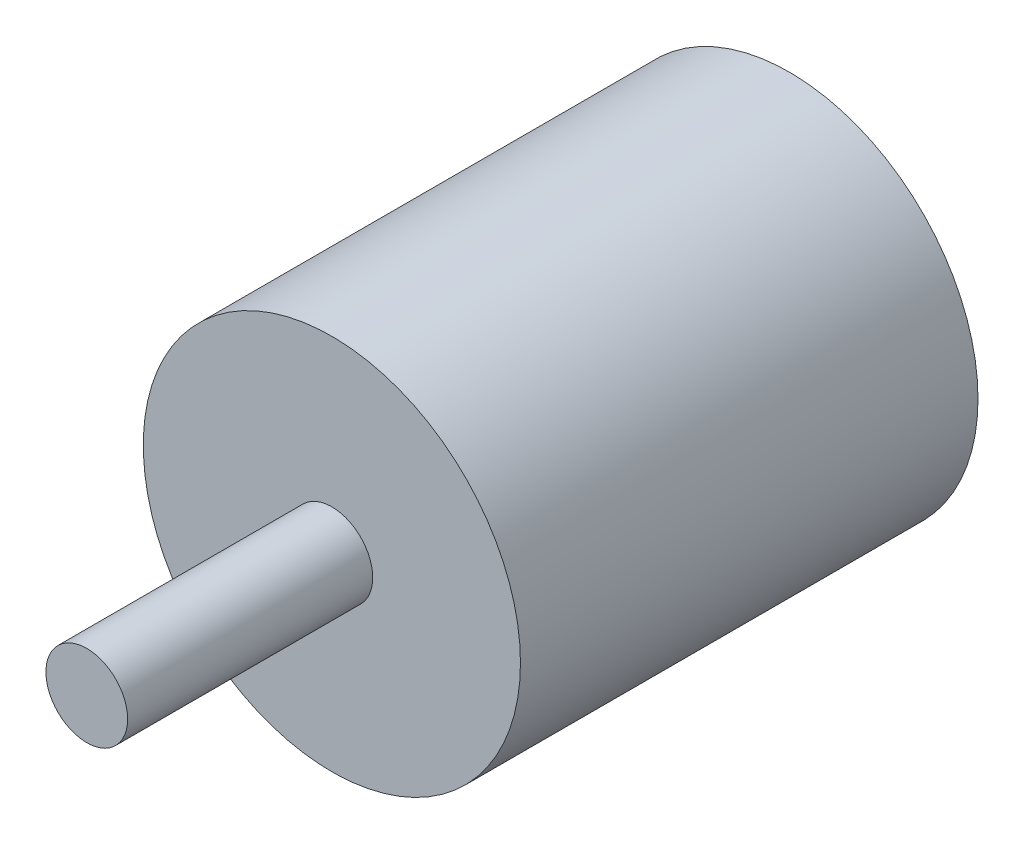
SolidWorks part; units mm, degrees
ref_plane "Front Plane" through (0, 0, 0) normal (0, 0, 1) x (1, 0, 0)
ref_plane "Top Plane" through (0, 0, 0) normal (0, 1, 0) x (1, 0, 0)
ref_plane "Right Plane" through (0, 0, 0) normal (1, 0, 0) x (0, 0, -1)
sketch "Sketch1" plane through (0, 0, 0) normal (0, 0, 1) x (1, 0, 0)
  circle A0 centre (0, 0) radius 13.85
  dimension "D1" = 27.7
extrude "Boss-Extrude1" add sketch "Sketch1" along normal blind 33.6
sketch "Sketch2" plane through (0, 0, 33.6) normal (0, 0, 1) x (1, 0, 0)
  circle A0 centre (0, 0) radius 3
  dimension "D1" = 6
extrude "Boss-Extrude2" add sketch "Sketch2" along normal blind 18
sketch "Sketch4" plane through (0, 0, 0) normal (0, 0, -1) x (-1, 0, 0)
  line L0 (9.515, 0) -> (-9.515, 0) construction
  line L1 (0, -7.5933) -> (0, 7.5933)
  circle A0 centre (-9.515, 0) radius 1.215
  circle A1 centre (9.515, 0) radius 1.215
  circle A2 centre (0, 7.5933) radius 1.5267
  circle A3 centre (0, -7.5933) radius 1.5267
  point P8 (0, 0)
  point P12 (0, 0)
  dimension "D1" = 16.6
  dimension "D2" = 21.46
  dimension "D3" = 13.66
  dimension "D4" = 18.24
  dimension "D5" = 15.1867
  dimension "D6" = 19.03
extrude "Cut-Extrude1" cut sketch "Sketch4" against normal blind 8
